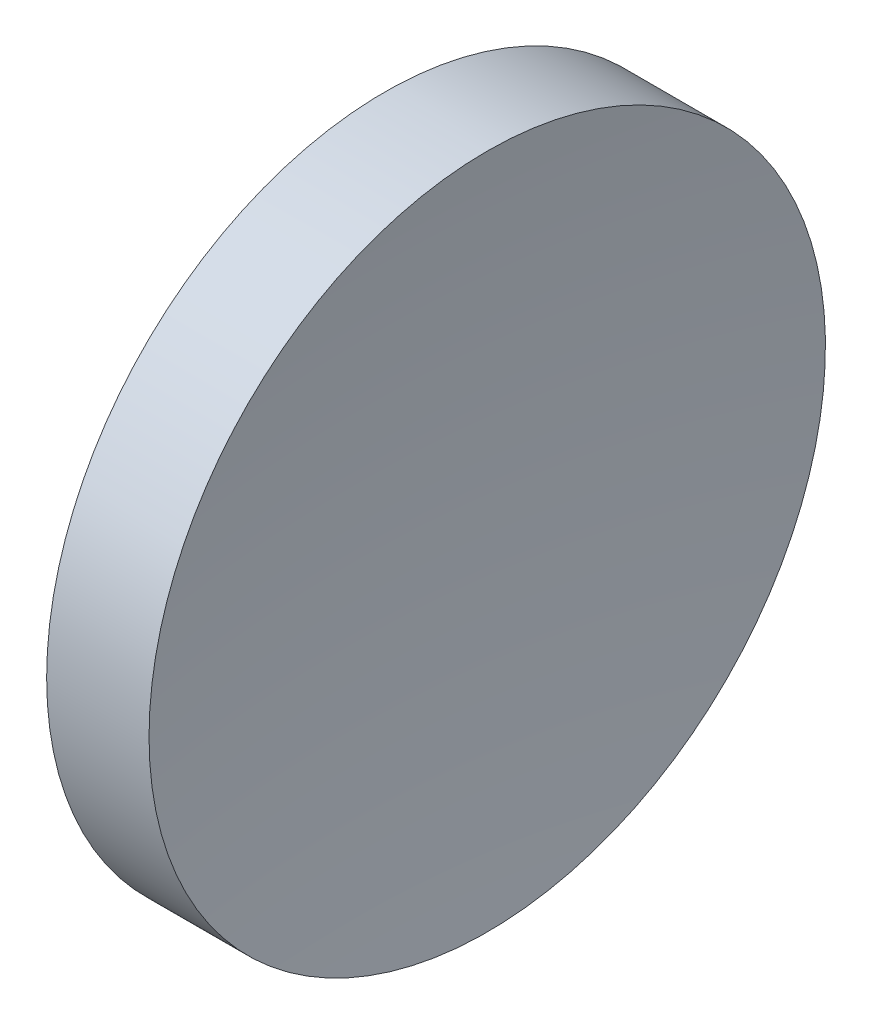
SolidWorks part; units mm, degrees
ref_plane "前视基准面" through (0, 0, 0) normal (0, 0, 1) x (1, 0, 0)
ref_plane "上视基准面" through (0, 0, 0) normal (0, 1, 0) x (1, 0, 0)
ref_plane "右视基准面" through (0, 0, 0) normal (1, 0, 0) x (0, 0, -1)
sketch "草图1" plane through (0, 0, 0) normal (0, 0, 1) x (1, 0, 0)
  line L0 (217.9703, 138.756) -> (265.5527, 138.756) construction
  line L1 (230.1996, 138.756) -> (230.1996, 176.256)
  line L2 (230.1996, 176.256) -> (241.5526, 176.256)
  line L3 (239.1996, 138.756) -> (230.1996, 138.756)
  arc A0 (241.5526, 176.256) -> (239.1996, 138.756) centre (539.1996, 138.756) ccw
revolve "旋转1" add sketch "草图1" angle 360 about L0
